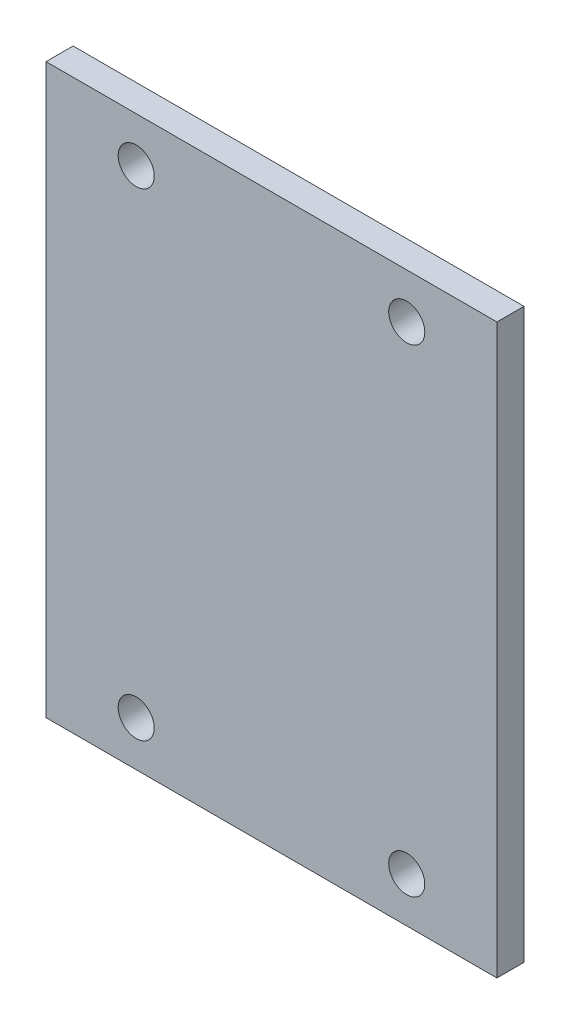
SolidWorks part; units mm, degrees
ref_plane "Alzado" through (0, 0, 0) normal (0, 0, 1) x (1, 0, 0)
ref_plane "Planta" through (0, 0, 0) normal (0, 1, 0) x (1, 0, 0)
ref_plane "Vista lateral" through (0, 0, 0) normal (1, 0, 0) x (0, 0, -1)
sketch "Croquis1" plane through (0, 0, 0) normal (0, 0, 1) x (1, 0, 0)
  line L0 (-1000, 0) -> (49000, 0) construction
  line L1 (-25, 31.5) -> (25, 31.5)
  line L2 (-25, 31.5) -> (-25, -31.5)
  line L3 (-25, -31.5) -> (25, -31.5)
  line L4 (25, 31.5) -> (25, -31.5)
  line L5 (-25, 31.5) -> (25, -31.5) construction
  line L6 (-25, -31.5) -> (25, 31.5) construction
  line L7 (0, -1000) -> (0, 49000) construction
  circle A0 centre (-15, -26.5) radius 2
  circle A1 centre (-15, 26.5) radius 2
  circle A2 centre (15, -26.5) radius 2
  circle A3 centre (15, 26.5) radius 2
  point P0 (0, 0)
  dimension "D3" = 4
  dimension "D1" = 63
  dimension "D2" = 50
  dimension "D4" = 5
  dimension "D5" = 10
extrude "Saliente-Extruir1" add sketch "Croquis1" along normal blind 3
